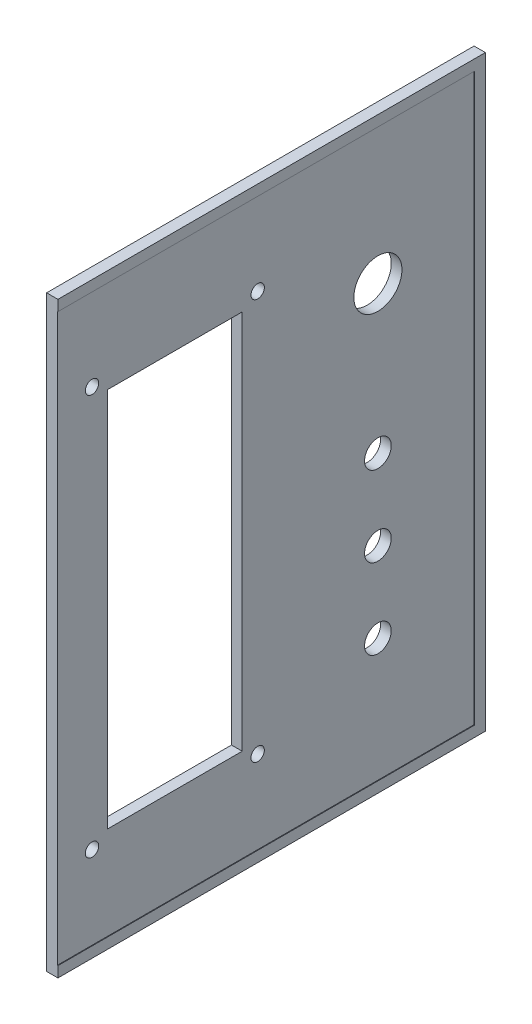
SolidWorks part; units mm, degrees
ref_plane "Front Plane" through (0, 0, 0) normal (0, 0, 1) x (1, 0, 0)
ref_plane "Top Plane" through (0, 0, 0) normal (0, 1, 0) x (1, 0, 0)
ref_plane "Right Plane" through (0, 0, 0) normal (1, 0, 0) x (0, 0, -1)
sketch "Sketch1" plane through (0, 0, 0) normal (0, 0, 1) x (1, 0, 0)
  line L1 (0, 0) -> (155, 0)
  line L2 (0, 0) -> (0, 110)
  line L3 (0, 110) -> (155, 110)
  line L4 (155, 0) -> (155, 110)
  dimension "D1" = 155
  dimension "D2" = 110
extrude "Boss-Extrude1" add sketch "Sketch1" along normal blind 80 contours L2 L1 L4 L3
sketch "Sketch2" plane through (0, 0, 80) normal (0, 0, 1) x (1, 0, 0)
  line L0 (0, 110) -> (2, 110) construction
  line L1 (0, 110) -> (155, 110) construction
  line L2 (0, 110) -> (0, 108) construction
  line L3 (0, 0) -> (0, 110) construction
  line L4 (155, 0) -> (155, 2) construction
  line L5 (155, 0) -> (155, 110) construction
  line L6 (155, 0) -> (153, 0) construction
  line L7 (0, 0) -> (155, 0) construction
  line L8 (0, 108) -> (2, 108) construction
  line L9 (2, 108) -> (2, 110) construction
  line L10 (155, 2) -> (153, 2) construction
  line L11 (153, 2) -> (153, 0) construction
  line L13 (153, 2) -> (2, 2)
  line L14 (153, 2) -> (153, 108)
  line L15 (153, 108) -> (2, 108)
  line L16 (2, 2) -> (2, 108)
  dimension "D1" = 2
  dimension "D2" = 2
  dimension "D3" = 2
  dimension "D4" = 2
extrude "Cut-Extrude1" cut sketch "Sketch2" against normal blind 78 contours L14 L13 L16 L15
sketch "Sketch3" plane through (0, 0, 2) normal (0, 0, 1) x (1, 0, 0)
  line L0 (2, 2) -> (6, 2) construction
  line L1 (153, 2) -> (2, 2) construction
  line L2 (153, 2) -> (149, 2) construction
  line L3 (2, 108) -> (6, 108) construction
  line L4 (153, 108) -> (2, 108) construction
  line L5 (2, 108) -> (2, 104.5) construction
  line L6 (2, 2) -> (2, 108) construction
  line L7 (149, 2) -> (149, 5.5) construction
  line L8 (2, 104.5) -> (6, 104.5) construction
  line L9 (6, 104.5) -> (6, 108) construction
  line L10 (6, 5.5) -> (10, 5.5) construction
  line L11 (6, 104.5) -> (149, 104.5)
  line L12 (6, 104.5) -> (6, 5.5)
  line L13 (6, 5.5) -> (149, 5.5)
  line L14 (149, 104.5) -> (149, 5.5)
  line L15 (10, 5.5) -> (10, 9.5) construction
  line L16 (149, 104.5) -> (145, 104.5) construction
  line L17 (145, 104.5) -> (145, 100.5) construction
  line L19 (10, 9.5) -> (145, 9.5)
  line L20 (10, 9.5) -> (10, 100.5)
  line L21 (10, 100.5) -> (145, 100.5)
  line L22 (145, 9.5) -> (145, 100.5)
  circle A0 centre (145, 100.5) radius 2.5
  circle A1 centre (145, 9.5) radius 2.5
  circle A2 centre (10, 9.5) radius 2.5
  circle A3 centre (10, 100.5) radius 2.5
  dimension "D10" = 5
  dimension "D11" = 5
  dimension "D12" = 5
  dimension "D13" = 5
  dimension "D1" = 4
  dimension "D2" = 3.5
  dimension "D3" = 4
  dimension "D4" = 4
  dimension "D5" = 3.5
  dimension "D6" = 4
  dimension "D7" = 4
  dimension "D8" = 4
  dimension "D9" = 4
extrude "Cut-Extrude2" cut sketch "Sketch3" against normal blind 2 contours A3 | A0 | A2 | A1
sketch "Sketch4" plane through (155, 0, 0) normal (1, 0, 0) x (0, 0, -1)
  line L1 (-53.75, 59.1) -> (-26.25, 59.1)
  line L3 (0, 55) -> (-80, 55) construction
  line L4 (0, 0) -> (0, 110) construction
  line L5 (-80, 0) -> (-80, 110) construction
  line L7 (-26.25, 105.9) -> (-26.25, 59.1)
  line L14 (-53.75, 105.9) -> (-26.25, 105.9)
  line L15 (-53.75, 105.9) -> (-53.75, 59.1)
  dimension "D1" = 46.8
  dimension "D2" = 27.5
sketch "Sketch7" plane through (0, 110, 0) normal (0, 1, 0) x (1, 0, 0)
  line L0 (0, -40) -> (155, -40) construction
  line L1 (0, -80) -> (0, 0) construction
  line L2 (155, -80) -> (155, 0) construction
  line L3 (77.5, 0) -> (77.5, -80) construction
  line L4 (0, 0) -> (155, 0) construction
  line L5 (0, -80) -> (155, -80) construction
  line L6 (110.52, -65.4) -> (95.28, -65.4) construction
  line L7 (44.48, -65.4) -> (110.52, -65.4)
  line L8 (44.48, -65.4) -> (44.48, -14.6)
  line L9 (44.48, -14.6) -> (110.52, -14.6)
  line L10 (110.52, -65.4) -> (110.52, -14.6)
  line L11 (44.48, -65.4) -> (110.52, -14.6) construction
  line L12 (44.48, -14.6) -> (110.52, -65.4) construction
  line L13 (95.28, -65.4) -> (95.28, -62.86) construction
  line L14 (110.52, -14.6) -> (95.28, -14.6) construction
  line L15 (44.48, -14.6) -> (44.48, -20.1445) construction
  line L16 (44.48, -65.4) -> (44.48, -47.62) construction
  line L17 (95.28, -14.6) -> (95.28, -17.14) construction
  line L18 (44.48, -65.4) -> (44.48, -19.68) construction
  circle A0 centre (44.48, -20.1445) radius 1.6
  circle A1 centre (95.28, -17.14) radius 1.6
  circle A2 centre (95.28, -62.86) radius 1.6
  circle A3 centre (44.48, -47.62) radius 1.6
  point P12 (77.5, -40)
  dimension "D9" = 3.2
  dimension "D10" = 3.2
  dimension "D11" = 3.2
  dimension "D12" = 3.2
  dimension "D1" = 66.04
  dimension "D2" = 50.8
  dimension "D3" = 15.24
  dimension "D4" = 2.54
  dimension "D5" = 15.24
  dimension "D6" = 2.54
  dimension "D7" = 17.78
  dimension "D8" = 45.72
extrude "Cut-Extrude7" cut sketch "Sketch7" against normal blind 2 contours A0 | A1 | A3 | A2
extrude "Cut-Extrude8" cut sketch "Sketch4" against normal blind 2
sketch "Sketch8" plane through (155, 0, 0) normal (1, 0, 0) x (0, 0, -1)
  line L0 (-80, 55) -> (0, 55) construction
  line L1 (-80, 0) -> (-80, 110) construction
  line L2 (0, 0) -> (0, 110) construction
  line L3 (0, 0) -> (-2, 0) construction
  line L4 (-80, 0) -> (0, 0) construction
  line L5 (-2, 0) -> (-2, 2) construction
  line L6 (-80, 0) -> (-78, 0) construction
  line L7 (-78, 0) -> (-78, 2) construction
  line L8 (-70, 2) -> (-70, 55)
  line L9 (-78, 2) -> (-74, 2)
  line L10 (-78, 2) -> (-78, 55)
  line L11 (-78, 55) -> (-74, 55)
  line L12 (-74, 2) -> (-74, 55)
  line L13 (-70, 2) -> (-66, 2)
  line L14 (-66, 2) -> (-66, 55)
  line L15 (-70, 55) -> (-66, 55)
  line L16 (-62, 2) -> (-62, 55)
  line L17 (-62, 2) -> (-58, 2)
  line L18 (-58, 2) -> (-58, 55)
  line L19 (-62, 55) -> (-58, 55)
  line L20 (-54, 2) -> (-54, 55)
  line L21 (-54, 2) -> (-50, 2)
  line L22 (-50, 2) -> (-50, 55)
  line L23 (-54, 55) -> (-50, 55)
  line L24 (-46, 2) -> (-46, 55)
  line L25 (-46, 2) -> (-42, 2)
  line L26 (-42, 2) -> (-42, 55)
  line L27 (-46, 55) -> (-42, 55)
  line L28 (-38, 2) -> (-38, 55)
  line L29 (-38, 2) -> (-34, 2)
  line L30 (-34, 2) -> (-34, 55)
  line L31 (-38, 55) -> (-34, 55)
  line L32 (-30, 2) -> (-30, 55)
  line L33 (-30, 2) -> (-26, 2)
  line L34 (-26, 2) -> (-26, 55)
  line L35 (-30, 55) -> (-26, 55)
  line L36 (-22, 2) -> (-22, 55)
  line L37 (-22, 2) -> (-18, 2)
  line L38 (-18, 2) -> (-18, 55)
  line L39 (-22, 55) -> (-18, 55)
  line L40 (-14, 2) -> (-14, 55)
  line L41 (-14, 2) -> (-10, 2)
  line L42 (-10, 2) -> (-10, 55)
  line L43 (-14, 55) -> (-10, 55)
  line L44 (-6, 2) -> (-6, 55)
  line L45 (-6, 2) -> (-2, 2)
  line L46 (-2, 2) -> (-2, 55)
  line L47 (-6, 55) -> (-2, 55)
  dimension "D1" = 2
  dimension "D2" = 2
  dimension "D3" = 2
  dimension "D4" = 2
  dimension "D5" = 4
extrude "Cut-Extrude9" cut sketch "Sketch8" against normal blind 2
sketch "Sketch9" plane through (0, 110, 0) normal (0, 1, 0) x (1, 0, 0)
  line L0 (0, -40) -> (155, -40) construction
  line L1 (0, -80) -> (0, 0) construction
  line L2 (155, -80) -> (155, 0) construction
  line L3 (155, -40) -> (120, -40) construction
  line L4 (120, -40) -> (120, -26) construction
  line L5 (120, -26) -> (113, -26) construction
  line L7 (113, -26) -> (127, -26)
  line L8 (113, -26) -> (113, -12)
  line L9 (113, -12) -> (127, -12)
  line L10 (127, -26) -> (127, -12)
  dimension "D1" = 35
  dimension "D2" = 14
  dimension "D3" = 7
  dimension "D4" = 14
  dimension "D5" = 14
extrude "Cut-Extrude10" cut sketch "Sketch9" against normal blind 2
sketch "Sketch10" plane through (0, 0, 0) normal (-1, 0, 0) x (0, 0, 1)
  line L0 (40, 110) -> (40, 0) construction
  line L1 (80, 110) -> (0, 110) construction
  line L2 (80, 0) -> (0, 0) construction
  line L3 (80, 55) -> (0, 55) construction
  line L4 (80, 0) -> (80, 110) construction
  line L5 (0, 0) -> (0, 110) construction
  line L6 (40, 55) -> (80, 55) construction
  line L7 (80, 55) -> (60, 55) construction
  line L8 (60, 55) -> (58, 55) construction
  line L9 (40, 95) -> (42.5, 95) construction
  line L10 (40, 15) -> (76, 15)
  line L11 (40, 15) -> (40, 95)
  line L12 (40, 95) -> (76, 95)
  line L13 (76, 15) -> (76, 95)
  line L14 (40, 15) -> (76, 95) construction
  line L15 (40, 95) -> (76, 15) construction
  line L16 (42.5, 95) -> (42.5, 92.5) construction
  line L17 (76, 15) -> (73.5, 15) construction
  line L18 (73.5, 15) -> (73.5, 17.5) construction
  line L19 (76, 15) -> (76, 19.4) construction
  line L20 (42.5, 92.5) -> (73.5, 92.5)
  line L21 (42.5, 92.5) -> (42.5, 17.5)
  line L22 (42.5, 17.5) -> (73.5, 17.5)
  line L23 (73.5, 92.5) -> (73.5, 17.5)
  line L24 (76, 19.4) -> (70.6, 19.4) construction
  line L25 (40, 95) -> (45.4, 95) construction
  line L26 (45.4, 95) -> (45.4, 90.6) construction
  line L28 (45.4, 90.6) -> (70.6, 90.6)
  line L29 (45.4, 90.6) -> (45.4, 19.4)
  line L30 (45.4, 19.4) -> (70.6, 19.4)
  line L31 (70.6, 90.6) -> (70.6, 19.4)
  circle A0 centre (73.5, 92.5) radius 1.25
  circle A1 centre (73.5, 17.5) radius 1.25
  circle A2 centre (42.5, 17.5) radius 1.25
  circle A3 centre (42.5, 92.5) radius 1.25
  dimension "D8" = 2.5
  dimension "D9" = 2.5
  dimension "D10" = 2.5
  dimension "D11" = 2.5
  dimension "D1" = 2
  dimension "D2" = 80
  dimension "D3" = 36
  dimension "D4" = 2.5
  dimension "D5" = 2.5
  dimension "D6" = 2.5
  dimension "D7" = 2.5
  dimension "D12" = 4.4
  dimension "D13" = 5.4
  dimension "D14" = 4.4
  dimension "D15" = 5.4
extrude "Cut-Extrude12" cut sketch "Sketch10" against normal blind 2 contours L31 L28 L29 L30 | A3 | A0 | A2 | A1
sketch "Sketch11" plane through (0, 0, 0) normal (-1, 0, 0) x (0, 0, 1)
  line L0 (40, 110) -> (40, 0) construction
  line L1 (80, 110) -> (0, 110) construction
  line L2 (80, 0) -> (0, 0) construction
  line L3 (20, 110) -> (20, 0) construction
  line L4 (0, 55) -> (0, 110) construction
  line L5 (0, 0) -> (0, 110) construction
  line L6 (40, 55) -> (0, 55) construction
  line L7 (0, 82.5) -> (40, 82.5) construction
  circle A0 centre (20, 55) radius 2.5
  circle A1 centre (20, 40) radius 2.5
  circle A2 centre (20, 25) radius 2.5
  circle A3 centre (20, 82.5) radius 4.5
  dimension "D1" = 5
  dimension "D3" = 9
  dimension "D2" = 3
extrude "Cut-Extrude13" cut sketch "Sketch11" against normal blind 2
sketch "Sketch12" plane through (0, 0, 80) normal (0, 0, 1) x (1, 0, 0)
  line L0 (2, 108) -> (2.1148, 110) construction
  line L1 (0, 110) -> (155, 110) construction
  line L2 (2.1148, 110) -> (2.1148, 0) construction
  line L3 (0, 0) -> (155, 0) construction
  line L5 (2.1148, 110) -> (155, 110)
  line L6 (2.1148, 110) -> (2.1148, 0)
  line L7 (2.1148, 0) -> (155, 0)
  line L8 (155, 110) -> (155, 0)
extrude "Cut-Extrude14" cut sketch "Sketch12" against normal blind 80
